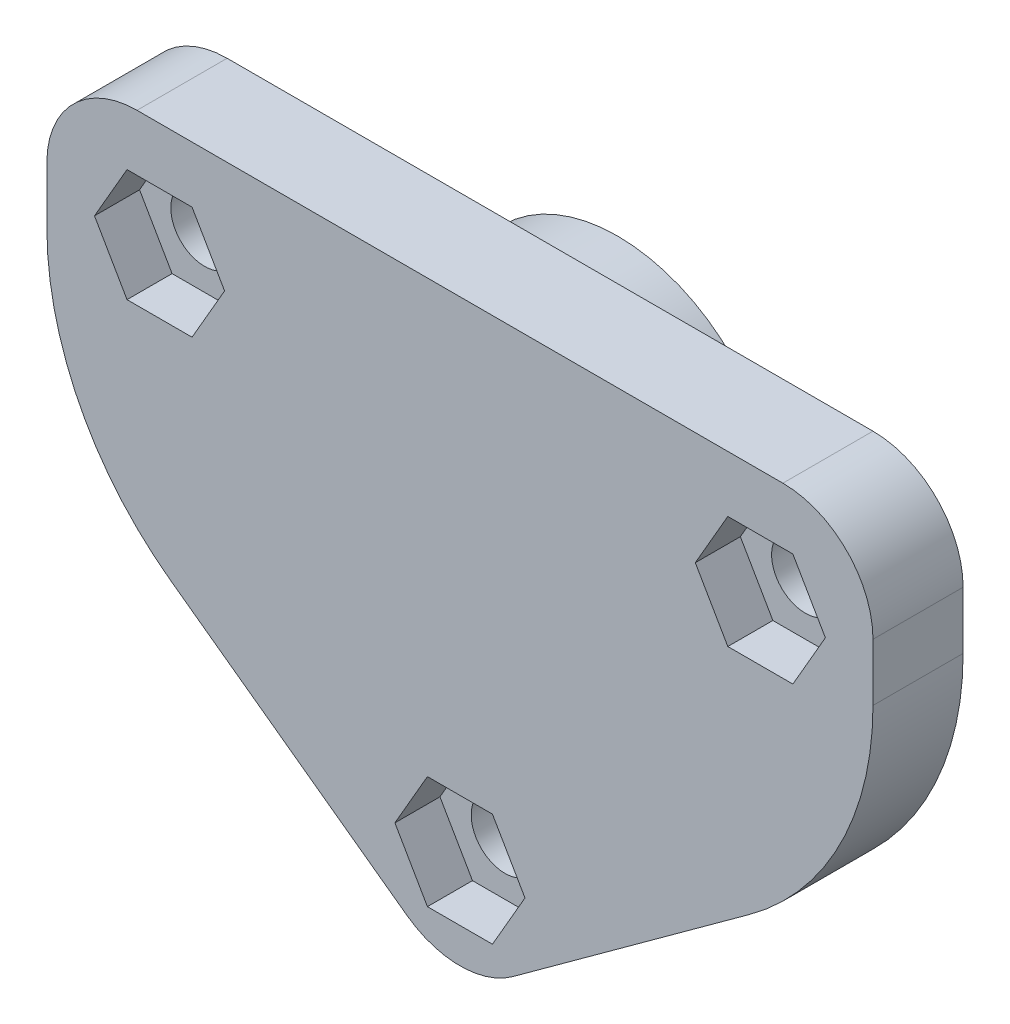
SolidWorks part; units mm, degrees
ref_plane "Plan de face" through (0, 0, 0) normal (0, 0, 1) x (1, 0, 0)
ref_plane "Plan de dessus" through (0, 0, 0) normal (0, 1, 0) x (1, 0, 0)
ref_plane "Plan de droite" through (0, 0, 0) normal (1, 0, 0) x (0, 0, -1)
sketch "Esquisse1" plane through (0, 0, 0) normal (0, 0, 1) x (1, 0, 0)
  line L0 (-55, 20) -> (-27.5, 0)
  line L1 (-55, 40) -> (0, 40)
  line L2 (-55, 40) -> (-55, 20)
  line L4 (0, 40) -> (0, 20)
  line L5 (-27.5, 0) -> (0, 20)
  circle A1 centre (-47.5, 32.5) radius 2.25
  circle A2 centre (-7.5, 32.5) radius 2.25
  circle A3 centre (-27.5, 7.5) radius 2.25
  dimension "D3" = 4.5
  dimension "D4" = 4.5
  dimension "D5" = 4.5
  dimension "D12" = 7.5
  dimension "D13" = 7.5
  dimension "D14" = 7.5
  dimension "D15" = 7.5
  dimension "D1" = 55
  dimension "D2" = 40
extrude "Boss.-Extru.1" add sketch "Esquisse1" along normal blind 6
fillet "Congé2" radius 6 3 edges at (-27.5, 0, 3) (-55, 40, 3) (0, 40, 3)
fillet "Congé3" radius 20 2 edges at (-55, 20, 3) (0, 20, 3)
sketch "Esquisse2" plane through (0, 0, 0) normal (0, 0, -1) x (-1, 0, 0)
  line L0 (0, 30.1845) -> (0, 34) construction
  line L1 (55, 34) -> (55, 30.1845) construction
  circle A0 centre (27.5, 27.5) radius 10.75
  circle A2 centre (27.5, 7.5) radius 2.25 construction
  dimension "D1" = 21.5
  dimension "D2" = 27.5
  dimension "D3" = 27.5
  dimension "D4" = 20
extrude "Boss.-Extru.2" add sketch "Esquisse2" along normal blind 4.5
sketch "Esquisse3" plane through (0, 0, -4.5) normal (0, 0, -1) x (-1, 0, 0)
  line L0 (27.5, 30.25) -> (27.5, 24.75)
  arc A0 (27.5, 30.25) -> (27.5, 24.75) centre (27.5, 27.5) ccw
  dimension "D1" = 5.5
revolve "Enlèvement de matière-Révolution5" cut sketch "Esquisse3" angle 360 about L0
sketch "Esquisse4" plane through (0, 0, 6) normal (0, 0, 1) x (1, 0, 0)
  line L1 (-43.1699, 32.5) -> (-45.3349, 36.25)
  line L2 (-45.3349, 36.25) -> (-49.6651, 36.25)
  line L3 (-49.6651, 36.25) -> (-51.8301, 32.5)
  line L4 (-51.8301, 32.5) -> (-49.6651, 28.75)
  line L5 (-49.6651, 28.75) -> (-45.3349, 28.75)
  line L6 (-45.3349, 28.75) -> (-43.1699, 32.5)
  line L7 (-11.8301, 32.5) -> (-9.6651, 28.75)
  line L8 (-9.6651, 28.75) -> (-5.3349, 28.75)
  line L9 (-5.3349, 28.75) -> (-3.1699, 32.5)
  line L10 (-3.1699, 32.5) -> (-5.3349, 36.25)
  line L11 (-5.3349, 36.25) -> (-9.6651, 36.25)
  line L12 (-9.6651, 36.25) -> (-11.8301, 32.5)
  line L13 (-23.1699, 7.5) -> (-25.3349, 11.25)
  line L14 (-25.3349, 11.25) -> (-29.6651, 11.25)
  line L15 (-29.6651, 11.25) -> (-31.8301, 7.5)
  line L16 (-31.8301, 7.5) -> (-29.6651, 3.75)
  line L17 (-29.6651, 3.75) -> (-25.3349, 3.75)
  line L18 (-25.3349, 3.75) -> (-23.1699, 7.5)
  circle A0 centre (-47.5, 32.5) radius 3.75 construction
  circle A1 centre (-7.5, 32.5) radius 3.75 construction
  circle A2 centre (-27.5, 7.5) radius 3.75 construction
  dimension "D1" = 7.5
  dimension "D2" = 7.5
  dimension "D3" = 7.5
extrude "Enlèv. mat.-Extru.1" cut sketch "Esquisse4" against normal blind 3
